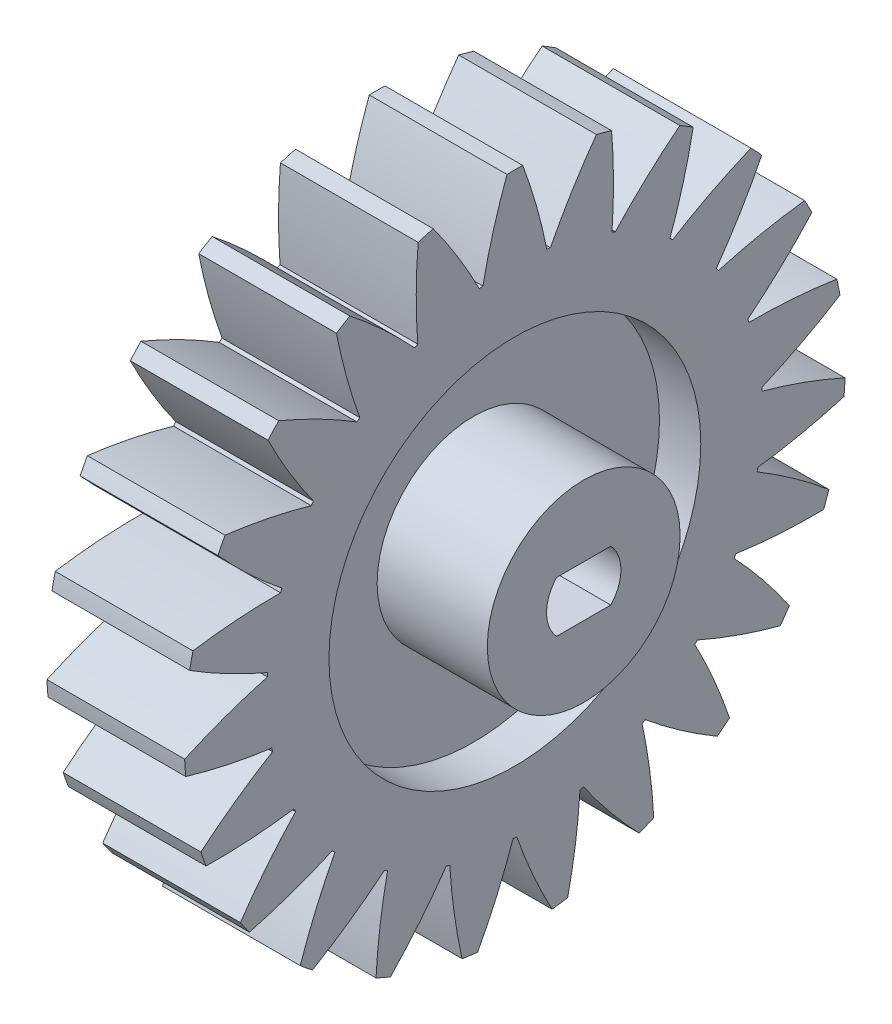
SolidWorks part; units mm, degrees
ref_plane "정면" through (0, 0, 0) normal (0, 0, 1) x (1, 0, 0)
ref_plane "윗면" through (0, 0, 0) normal (0, 1, 0) x (1, 0, 0)
ref_plane "우측면" through (0, 0, 0) normal (1, 0, 0) x (0, 0, -1)
sketch "스케치3" plane through (0, 0, 0) normal (0, 0, 1) x (1, 0, 0)
  line L0 (-44.782, 0) -> (54.3593, 0) construction
  line L1 (-5, 18) -> (5, 18)
  line L3 (5, 0) -> (-5, 0)
  line L4 (-5, 0) -> (-5, 7)
  line L5 (-5, 7) -> (-2, 7)
  line L6 (-2, 7) -> (-2, 13.5)
  line L7 (-2, 13.5) -> (-5, 13.5)
  line L8 (-5, 13.5) -> (-5, 18)
  line L9 (0, 34.3131) -> (0, -34.9075) construction
  line L10 (5, 13.5) -> (5, 18)
  line L11 (2, 13.5) -> (5, 13.5)
  line L12 (2, 7) -> (2, 13.5)
  line L13 (5, 7) -> (2, 7)
  line L14 (5, 0) -> (5, 7)
  point P6 (0, 18)
  point P19 (0, 0)
  dimension "D1" = 36
  dimension "D2" = 27
  dimension "D3" = 14
  dimension "D4" = 10
  dimension "D5" = 4
revolve "회전1" add sketch "스케치3" angle 360 mid plane about L0
sketch "스케치4" plane through (5, 0, 0) normal (1, 0, 0) x (0, 0, -1)
  line L0 (-30.6336, 0) -> (34.07, 0) construction
  line L1 (0, 24) -> (0, -32.3013) construction
  line L2 (-1.57, 20.9412) -> (-1.57, -32.3013) construction
  line L3 (-2.32, 17.8499) -> (-2.32, -32.3013) construction
  line L4 (-0.57, 23.9932) -> (-0.57, -32.3013)
  line L5 (-0.57, 36.6372) -> (-0.57, -32.3013) construction
  line L6 (-2.32, 36.6372) -> (-2.32, -32.3013) construction
  line L7 (-1.57, 36.6372) -> (-1.57, -32.3013) construction
  line L8 (0, 36.6372) -> (0, -32.3013) construction
  arc A1 (-21, 0) -> (21, 0) centre (0, 0) ccw construction
  circle A2 centre (0, 0) radius 18 construction
  arc A3 (-0.57, 23.9932) -> (-2.32, 17.8499) centre (37.5455, 9.8147) ccw
  circle A4 centre (0, 0) radius 24
  arc A5 (-24, 0) -> (24, 0) centre (0, 0) ccw
  arc A6 (0.57, 23.9932) -> (2.32, 17.8499) centre (-37.5455, 9.8147) cw
  circle A7 centre (0, 0) radius 24 construction
  circle A8 centre (0, 0) radius 21 construction
  arc A9 (0.57, 23.9932) -> (-0.57, 23.9932) centre (0, 0) ccw
  arc A10 (1.57, 20.9412) -> (-1.57, 20.9412) centre (0, 0) ccw construction
  point P5 (-2.32, 17.8499)
  point P19 (-1.57, 20.9412)
  circle M2 centre (0, 0) radius 18
  dimension "D1" = 6
  dimension "D2" = 1.57
  dimension "D3" = 0.75
  dimension "D4" = 1
  dimension "D5" = 3
extrude "보스-돌출1" add sketch "스케치4" against normal through all contours A6 A9 L4 M2 | L4 A3 M2
pattern_circular "원형 패턴1" count 23 over 360 about axis through (0, 0, 0) along (1, 0, 0) of "보스-돌출1"
sketch "스케치6" plane through (5, 0, 0) normal (1, 0, 0) x (0, 0, -1)
  circle A0 centre (0, 0) radius 7
extrude "보스-돌출2" add sketch "스케치6" along normal blind 5
sketch "스케치7" plane through (-5, 0, 0) normal (-1, 0, 0) x (0, 0, 1)
  line L1 (1.9666, -1.85) -> (-1.9666, -1.85)
  line L3 (1.9666, 1.85) -> (-1.9666, 1.85)
  arc A0 (-1.9666, 1.85) -> (-1.9666, -1.85) centre (0, 0) ccw
  arc A1 (1.9666, -1.85) -> (1.9666, 1.85) centre (0, 0) ccw
  dimension "D1" = 5.4
extrude "컷-돌출2" cut sketch "스케치7" against normal through all
